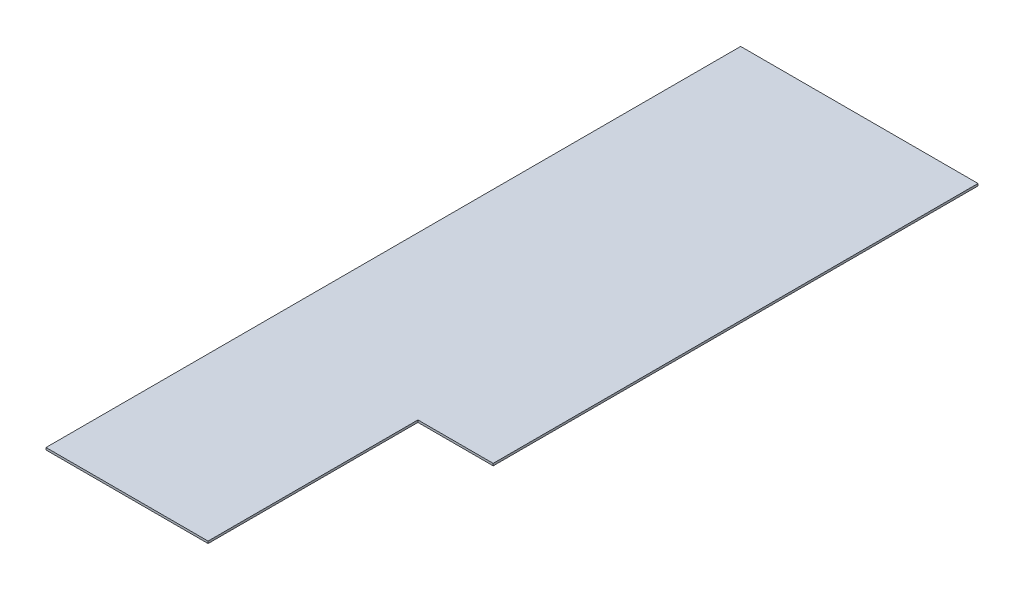
SolidWorks part; units mm, degrees
ref_plane "Front Plane" through (0, 0, 0) normal (0, 0, 1) x (1, 0, 0)
ref_plane "Top Plane" through (0, 0, 0) normal (0, 1, 0) x (1, 0, 0)
ref_plane "Right Plane" through (0, 0, 0) normal (1, 0, 0) x (0, 0, -1)
sketch "Sketch1" plane through (0, 0, 0) normal (0, 1, 0) x (1, 0, 0)
  line L1 (-260.35, 0) -> (260.35, 0)
  line L2 (-260.35, 0) -> (-260.35, 1524)
  line L3 (-260.35, 1524) -> (260.35, 1524)
  line L4 (260.35, 0) -> (260.35, 1524)
  point P5 (0, 0)
  dimension "D1" = 1524
  dimension "D2" = 520.7
extrude "Boss-Extrude1" add sketch "Sketch1" along normal blind 4.7752
ref_plane "Plane1" through (0, 0, 0) normal (1, 0, 0) x (0, 0, -1)
sketch "Sketch2" plane through (0, 4.7752, 0) normal (0, 1, 0) x (1, 0, 0)
  line L1 (260.35, 0) -> (95.25, 0)
  line L2 (260.35, 0) -> (260.35, 460.375)
  line L3 (260.35, 460.375) -> (95.25, 460.375)
  line L4 (95.25, 0) -> (95.25, 460.375)
  dimension "D1" = 165.1
  dimension "D2" = 460.375
extrude "Cut-Extrude1" cut sketch "Sketch2" against normal through all
